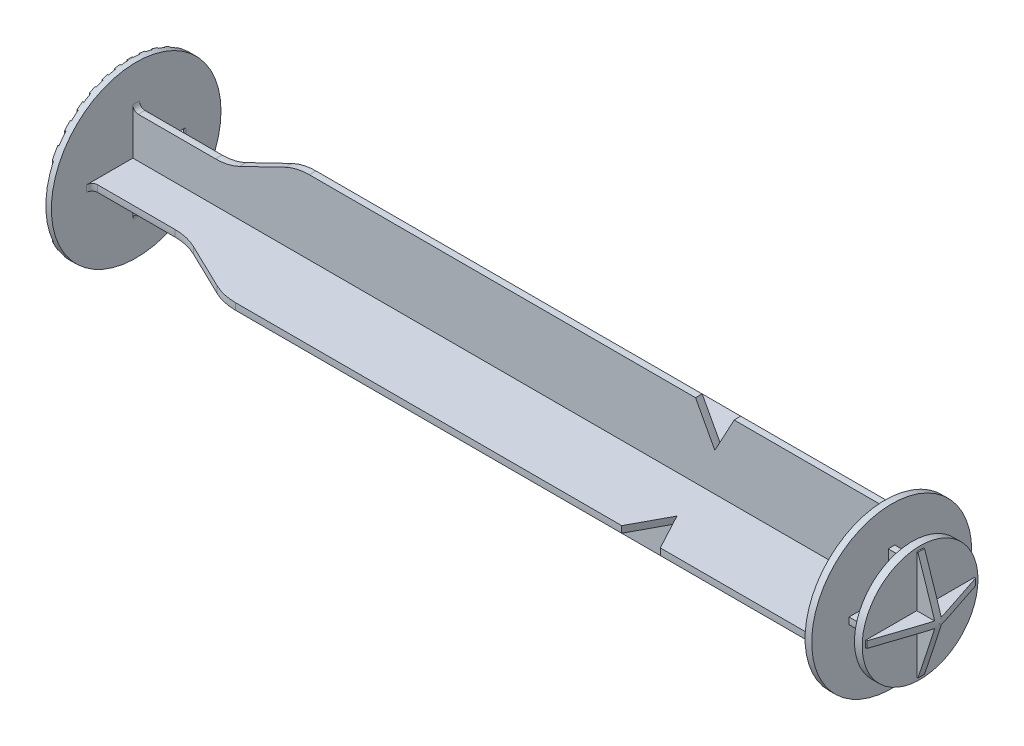
SolidWorks part; units mm, degrees
material "Polyethylene Cross-Linked"
ref_plane "Front Plane" through (0, 0, 0) normal (0, 0, 1) x (1, 0, 0)
ref_plane "Top Plane" through (0, 0, 0) normal (0, 1, 0) x (1, 0, 0)
ref_plane "Right Plane" through (0, 0, 0) normal (1, 0, 0) x (0, 0, -1)
sketch "Sketch1" plane through (0, 0, 0) normal (0, 0, 1) x (1, 0, 0)
  line L0 (146.8, 0) -> (-146.8, 0) construction
  line L1 (0, 0) -> (0, 15.375)
  line L2 (0, 15.375) -> (1.2, 15.375)
  line L3 (1.2, 15.375) -> (1.2, 9)
  line L4 (2.2, 8) -> (16.2, 8)
  line L5 (20.549, 8.9952) -> (28.851, 13.0048)
  line L6 (33.2, 14) -> (103.2, 14)
  line L7 (103.2, 14) -> (106.7, 7.5)
  line L8 (106.7, 7.5) -> (110.2, 14)
  line L9 (110.2, 14) -> (136.95, 14)
  line L10 (136.95, 14) -> (136.95, 14.5)
  line L11 (136.95, 14.5) -> (138.15, 14.5)
  line L12 (138.15, 14.5) -> (138.15, 7.75)
  line L13 (138.15, 7.75) -> (141.9, 7.75)
  line L14 (141.9, 7.75) -> (141.9, 10.5)
  line L15 (141.9, 10.5) -> (143.3, 10.5)
  line L16 (143.3, 10.5) -> (146.8, 0)
  line L17 (0, 0) -> (146.8, 0)
  arc A0 (1.2, 9) -> (2.2, 8) centre (2.2, 9) ccw
  arc A1 (28.851, 13.0048) -> (33.2, 14) centre (33.2, 4) cw
  arc A2 (16.2, 8) -> (20.549, 8.9952) centre (16.2, 18) ccw
  point P4 (0, 0)
  dimension "D14" = 1
  dimension "D15" = 10
  dimension "D1" = 1.2
  dimension "D2" = 135.75
  dimension "D3" = 30.75
  dimension "D4" = 16
  dimension "D5" = 105.5
  dimension "D6" = 15
  dimension "D7" = 7
  dimension "D8" = 28
  dimension "D9" = 29
  dimension "D10" = 15.5
  dimension "D11" = 21
  dimension "D12" = 146.8
  dimension "D13" = 3.75
  dimension "D16" = 15
  dimension "D17" = 32
  dimension "D18" = 3.5
revolve "Revolve1" add sketch "Sketch1" angle 360 about L0
sketch "Sketch2" plane through (1.2, 0, 0) normal (1, 0, 0) x (0, 0, -1)
  line L0 (17.7295, 0) -> (-17.7295, 0) construction
  line L1 (0, -17.5817) -> (0, 17.5817) construction
  line L2 (-0.6, 15.3633) -> (-0.6, 0.6)
  line L3 (-0.6, 0.6) -> (-15.3633, 0.6)
  line L4 (0.6, 0.6) -> (0.6, 15.3633)
  line L5 (15.3633, 0.6) -> (0.6, 0.6)
  line L6 (0.6, -0.6) -> (15.3633, -0.6)
  line L7 (0.6, -15.3633) -> (0.6, -0.6)
  line L8 (-0.6, -0.6) -> (-0.6, -15.3633)
  line L9 (-15.3633, -0.6) -> (-0.6, -0.6)
  circle A0 centre (0, 0) radius 15.375 construction
  arc A1 (-15.3633, 0.6) -> (-15.3633, -0.6) centre (0, 0) ccw
  arc A2 (0.6, 15.3633) -> (-0.6, 15.3633) centre (0, 0) ccw
  arc A3 (15.3633, -0.6) -> (15.3633, 0.6) centre (0, 0) ccw
  arc A4 (-0.6, -15.3633) -> (0.6, -15.3633) centre (0, 0) ccw
  point P5 (0, 0)
  point P9 (0, 0)
  point P27 (0, 0)
  dimension "D3" = 1.2
  dimension "D2" = 4
extrude "Cut-Extrude1" cut sketch "Sketch2" along normal up to surface (135.75 mm away) flip side to cut up to face at (136.95, 0, -14)
sketch "Sketch3" plane through (0, 0, 0) normal (-1, 0, 0) x (0, 0, 1)
  line L0 (2.75, -15.3669) -> (1.75, -15.3669)
  line L1 (0.5, -15.3669) -> (-0.5, -15.3669)
  line L2 (0.5, -15.3669) -> (0.5, 15.3669)
  line L3 (0.5, 15.3669) -> (-0.5, 15.3669)
  line L4 (-0.5, -15.3669) -> (-0.5, 15.3669)
  line L5 (0.5, -15.3669) -> (-0.5, 15.3669) construction
  line L6 (0.5, 15.3669) -> (-0.5, -15.3669) construction
  line L7 (1.75, -15.3669) -> (1.75, 15.3669)
  line L8 (2.75, 15.3669) -> (1.75, 15.3669)
  line L9 (2.75, -15.3669) -> (2.75, 15.3669)
  line L10 (5, -15.3669) -> (4, -15.3669)
  line L11 (4, -15.3669) -> (4, 15.3669)
  line L12 (5, 15.3669) -> (4, 15.3669)
  line L13 (5, -15.3669) -> (5, 15.3669)
  line L14 (7.25, -15.3669) -> (6.25, -15.3669)
  line L15 (6.25, -15.3669) -> (6.25, 15.3669)
  line L16 (7.25, 15.3669) -> (6.25, 15.3669)
  line L17 (7.25, -15.3669) -> (7.25, 15.3669)
  line L18 (9.5, -15.3669) -> (8.5, -15.3669)
  line L19 (8.5, -15.3669) -> (8.5, 15.3669)
  line L20 (9.5, 15.3669) -> (8.5, 15.3669)
  line L21 (9.5, -15.3669) -> (9.5, 15.3669)
  line L22 (11.75, -15.3669) -> (10.75, -15.3669)
  line L23 (10.75, -15.3669) -> (10.75, 15.3669)
  line L24 (11.75, 15.3669) -> (10.75, 15.3669)
  line L25 (11.75, -15.3669) -> (11.75, 15.3669)
  line L26 (14, -15.3669) -> (13, -15.3669)
  line L27 (13, -15.3669) -> (13, 15.3669)
  line L28 (14, 15.3669) -> (13, 15.3669)
  line L29 (14, -15.3669) -> (14, 15.3669)
  line L30 (-1.75, -15.3669) -> (-2.75, -15.3669)
  line L31 (-2.75, -15.3669) -> (-2.75, 15.3669)
  line L32 (-1.75, 15.3669) -> (-2.75, 15.3669)
  line L33 (-1.75, -15.3669) -> (-1.75, 15.3669)
  line L34 (-4, -15.3669) -> (-5, -15.3669)
  line L35 (-5, -15.3669) -> (-5, 15.3669)
  line L36 (-4, 15.3669) -> (-5, 15.3669)
  line L37 (-4, -15.3669) -> (-4, 15.3669)
  line L38 (-6.25, -15.3669) -> (-7.25, -15.3669)
  line L39 (-7.25, -15.3669) -> (-7.25, 15.3669)
  line L40 (-6.25, 15.3669) -> (-7.25, 15.3669)
  line L41 (-6.25, -15.3669) -> (-6.25, 15.3669)
  line L42 (-8.5, -15.3669) -> (-9.5, -15.3669)
  line L43 (-9.5, -15.3669) -> (-9.5, 15.3669)
  line L44 (-8.5, 15.3669) -> (-9.5, 15.3669)
  line L45 (-8.5, -15.3669) -> (-8.5, 15.3669)
  line L46 (-10.75, -15.3669) -> (-11.75, -15.3669)
  line L47 (-11.75, -15.3669) -> (-11.75, 15.3669)
  line L48 (-10.75, 15.3669) -> (-11.75, 15.3669)
  line L49 (-10.75, -15.3669) -> (-10.75, 15.3669)
  line L50 (-13, -15.3669) -> (-14, -15.3669)
  line L51 (-14, -15.3669) -> (-14, 15.3669)
  line L52 (-13, 15.3669) -> (-14, 15.3669)
  line L53 (-13, -15.3669) -> (-13, 15.3669)
  circle A0 centre (0, 0) radius 15.375 construction
  point P0 (0, 0)
  dimension "D1" = 1
  dimension "D3" = 2.25
  dimension "D2" = 7
  dimension "D4" = 7
extrude "Cut-Extrude2" cut sketch "Sketch3" against normal blind 0.2 flip side to cut
sketch "Sketch4" plane through (138.15, 0, 0) normal (1, 0, 0) x (0, 0, -1)
  line L8 (0.6, 0.6) -> (0.6, 15.3633)
  line L9 (-0.6, 15.3633) -> (-0.6, 0.6)
  line L10 (-0.6, 0.6) -> (-15.3633, 0.6)
  line L11 (-15.3633, -0.6) -> (-0.6, -0.6)
  line L12 (-0.6, -0.6) -> (-0.6, -15.3633)
  line L13 (0.6, -15.3633) -> (0.6, -0.6)
  line L14 (0.6, -0.6) -> (15.3633, -0.6)
  line L15 (15.3633, 0.6) -> (0.6, 0.6)
  line L16 (0.6, 0.6) -> (0.6, 15.3633)
  line L17 (-0.6, 15.3633) -> (-0.6, 0.6)
  line L18 (-0.6, 0.6) -> (-15.3633, 0.6)
  line L19 (-15.3633, -0.6) -> (-0.6, -0.6)
  line L20 (-0.6, -0.6) -> (-0.6, -15.3633)
  line L21 (0.6, -15.3633) -> (0.6, -0.6)
  line L22 (0.6, -0.6) -> (15.3633, -0.6)
  line L23 (15.3633, 0.6) -> (0.6, 0.6)
  arc A4 (0.6, 15.3633) -> (-0.6, 15.3633) centre (0, 0) ccw
  arc A5 (-15.3633, 0.6) -> (-15.3633, -0.6) centre (0, 0) ccw
  arc A6 (-0.6, -15.3633) -> (0.6, -15.3633) centre (0, 0) ccw
  arc A7 (15.3633, -0.6) -> (15.3633, 0.6) centre (0, 0) ccw
  arc A8 (0.6, 15.3633) -> (-0.6, 15.3633) centre (0, 0) ccw
  arc A9 (-15.3633, 0.6) -> (-15.3633, -0.6) centre (0, 0) ccw
  arc A10 (-0.6, -15.3633) -> (0.6, -15.3633) centre (0, 0) ccw
  arc A11 (15.3633, -0.6) -> (15.3633, 0.6) centre (0, 0) ccw
  dimension "D1" = 0
extrude "Cut-Extrude3" cut sketch "Sketch4" along normal up to surface (3.75 mm away) flip side to cut up to face at (141.9, 0, -7.75)
ref_plane "Plane1" through (146.8, 0, 0) normal (1, 0, 0) x (0, 0, -1)
sketch "Sketch5" plane through (146.8, 0, 0) normal (1, 0, 0) x (0, 0, -1)
  line L8 (0.6, 0.6) -> (0.6, 15.3633)
  line L9 (-0.6, 15.3633) -> (-0.6, 0.6)
  line L10 (-0.6, 0.6) -> (-15.3633, 0.6)
  line L11 (-15.3633, -0.6) -> (-0.6, -0.6)
  line L12 (-0.6, -0.6) -> (-0.6, -15.3633)
  line L13 (0.6, -15.3633) -> (0.6, -0.6)
  line L14 (0.6, -0.6) -> (15.3633, -0.6)
  line L15 (15.3633, 0.6) -> (0.6, 0.6)
  line L16 (0.6, 0.6) -> (0.6, 9.8568)
  line L17 (-0.6, 9.8568) -> (-0.6, 0.6)
  line L18 (-0.6, 0.6) -> (-9.8568, 0.6)
  line L19 (-9.8568, -0.6) -> (-0.6, -0.6)
  line L20 (-0.6, -0.6) -> (-0.6, -9.8568)
  line L21 (0.6, -9.8568) -> (0.6, -0.6)
  line L22 (0.6, -0.6) -> (9.8568, -0.6)
  line L23 (9.8568, 0.6) -> (0.6, 0.6)
  arc A0 (-9.8568, 0.6) -> (-9.8568, -0.6) centre (0, 0) ccw
  arc A1 (9.8568, -0.6) -> (9.8568, 0.6) centre (0, 0) ccw
  arc A2 (0.6, 9.8568) -> (-0.6, 9.8568) centre (0, 0) ccw
  arc A3 (-0.6, -9.8568) -> (0.6, -9.8568) centre (0, 0) ccw
  arc A4 (0.6, 15.3633) -> (-0.6, 15.3633) centre (0, 0) ccw
  arc A5 (-15.3633, 0.6) -> (-15.3633, -0.6) centre (0, 0) ccw
  arc A6 (-0.6, -15.3633) -> (0.6, -15.3633) centre (0, 0) ccw
  arc A7 (15.3633, -0.6) -> (15.3633, 0.6) centre (0, 0) ccw
  dimension "D2" = 19.75
  dimension "D1" = 0
extrude "Cut-Extrude4" cut sketch "Sketch5" against normal blind 3.5 flip side to cut
